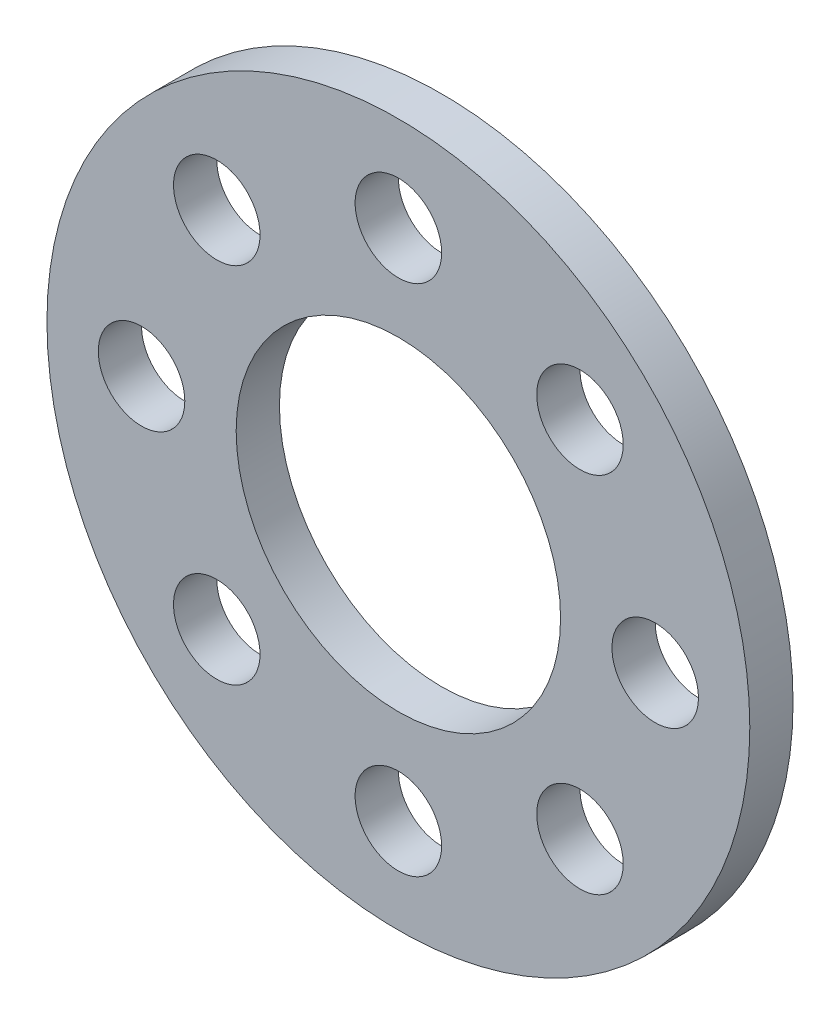
SolidWorks part; units mm, degrees
ref_plane "Plan de face" through (0, 0, 0) normal (0, 0, 1) x (1, 0, 0)
ref_plane "Plan de dessus" through (0, 0, 0) normal (0, 1, 0) x (1, 0, 0)
ref_plane "Plan de droite" through (0, 0, 0) normal (1, 0, 0) x (0, 0, -1)
sketch "Esquisse1" plane through (0, 0, 0) normal (0, 0, 1) x (1, 0, 0)
  line L0 (0, 0) -> (0, 16.25) construction
  circle A0 centre (0, 0) radius 16.25
  circle A1 centre (0, 0) radius 7.5
  circle A2 centre (0, 0) radius 11.875 construction
  circle A3 centre (0, 11.875) radius 2
  circle A4 centre (8.3969, 8.3969) radius 2
  circle A5 centre (11.875, 0) radius 2
  circle A6 centre (8.3969, -8.3969) radius 2
  circle A7 centre (0, -11.875) radius 2
  circle A8 centre (-8.3969, -8.3969) radius 2
  circle A9 centre (-11.875, 0) radius 2
  circle A10 centre (-8.3969, 8.3969) radius 2
  point P24 (0, 0)
  dimension "D1" = 32.5
  dimension "D2" = 15
  dimension "D3" = 4
  dimension "D4" = 8.75
  dimension "D5" = 4.375
  dimension "D6" = 8
extrude "Boss.-Extru.1" add sketch "Esquisse1" along normal blind 2
